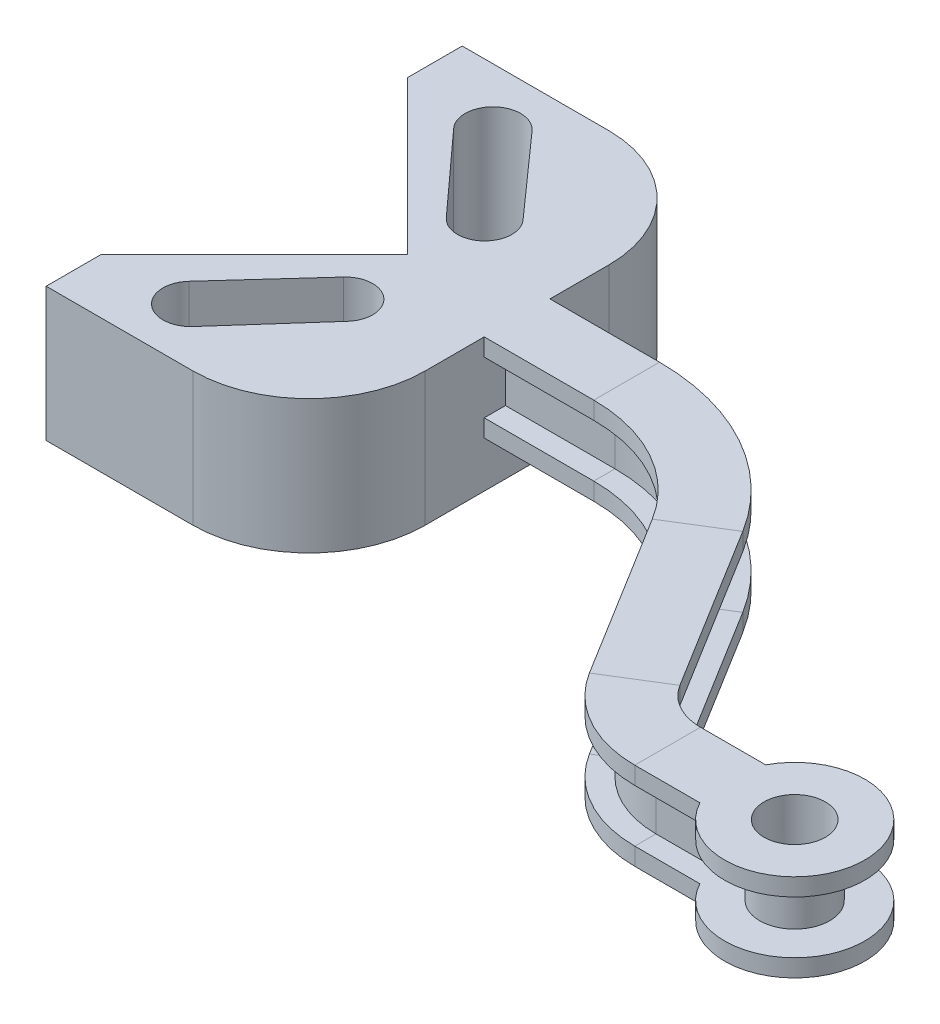
SolidWorks part; units mm, degrees
ref_plane "Front Plane" through (0, 0, 0) normal (0, 0, 1) x (1, 0, 0)
ref_plane "Top Plane" through (0, 0, 0) normal (0, 1, 0) x (1, 0, 0)
ref_plane "Right Plane" through (0, 0, 0) normal (1, 0, 0) x (0, 0, -1)
sketch "Sketch1" plane through (0, 0, 0) normal (0, 1, 0) x (1, 0, 0)
  line L0 (484.4371, 0) -> (-616.5563, 0) construction
  line L1 (-300, -132.5) -> (-132.5, -132.5)
  line L2 (-300, -132.5) -> (-300, -70.1185)
  line L3 (-300, -70.1185) -> (-125, 104.8815)
  line L4 (-125, 104.8815) -> (-610.7916, 104.8815) construction
  line L5 (-300, 342.2631) -> (-132.5, 342.2631)
  line L6 (-300, 342.2631) -> (-300, 279.8815)
  line L7 (-300, 279.8815) -> (-125, 104.8815)
  line L8 (0, 209.7631) -> (0, 0)
  arc A0 (-132.5, -132.5) -> (0, 0) centre (-132.5, 0) ccw
  arc A1 (-132.5, 342.2631) -> (0, 209.7631) centre (-132.5, 209.7631) cw
  dimension "D2" = 132.5
  dimension "D1" = 237.5
  dimension "D3" = 300
  dimension "D4" = 90
  dimension "D5" = 175
extrude "Boss-Extrude1" add sketch "Sketch1" along normal blind 152.5
sketch "Sketch2" plane through (0, 152.5, 0) normal (0, 1, 0) x (1, 0, 0)
  line L0 (-300, -70.1185) -> (-300, -132.5) construction
  line L2 (-300, -132.5) -> (-132.5, -132.5) construction
  line L3 (-223.4478, -46.1823) -> (-139.3618, 46.3059)
  line L4 (-93.2582, 4.853) -> (-176.3183, -88.5576)
  line L5 (-125, 104.8815) -> (188.3086, 104.8815) construction
  line L6 (-93.2582, 204.9101) -> (-176.3183, 298.3207)
  line L7 (-223.4478, 255.9454) -> (-139.3618, 163.4572)
  arc A0 (-223.4478, -46.1823) -> (-176.3183, -88.5576) centre (-200, -67.5) ccw
  arc A1 (-93.2582, 4.853) -> (-139.3618, 46.3059) centre (-116.4244, 25.4522) ccw
  arc A2 (-93.2582, 204.9101) -> (-139.3618, 163.4572) centre (-116.4244, 184.3109) cw
  arc A3 (-223.4478, 255.9454) -> (-176.3183, 298.3207) centre (-200, 277.2631) cw
  point P0 (-200, -67.5)
  point P1 (-116.4244, 25.4522)
  dimension "D4" = 62
  dimension "D1" = 100
  dimension "D2" = 65
  dimension "D3" = 125
extrude "Cut-Extrude1" cut sketch "Sketch2" against normal through all
sketch "Sketch3" plane through (0, 0, 0) normal (1, 0, 0) x (0, 0, -1)
  line L0 (104.8815, 152.5) -> (104.8815, -55.0634) construction
  line L2 (67.3815, 152.5) -> (142.3815, 152.5)
  line L3 (142.3815, 152.5) -> (142.3815, 132.5)
  line L4 (142.3815, 132.5) -> (118.1669, 132.5)
  line L5 (118.1669, 132.5) -> (118.1669, 72.5)
  line L6 (118.1669, 72.5) -> (142.3815, 72.5)
  line L7 (142.3815, 72.5) -> (142.3815, 52.5)
  line L8 (142.3815, 52.5) -> (67.3815, 52.5)
  line L9 (67.3815, 72.5) -> (67.3815, 52.5)
  line L10 (91.5962, 72.5) -> (67.3815, 72.5)
  line L11 (91.5962, 132.5) -> (91.5962, 72.5)
  line L12 (67.3815, 132.5) -> (91.5962, 132.5)
  line L13 (67.3815, 152.5) -> (67.3815, 132.5)
  point P11 (104.8815, 52.5)
  point P16 (0, 0)
  point P17 (0, 0)
  dimension "D1" = 37.5
  dimension "D2" = 20
  dimension "D3" = 100
sketch "Sketch4" plane through (0, 0, 0) normal (0, 1, 0) x (1, 0, 0)
  line L0 (0, 104.8815) -> (125, 104.8815)
  line L1 (307.8767, 2.9351) -> (424.1086, -185.083)
  line L2 (509.1676, -232.5) -> (654.1676, -232.5)
  line L3 (-300, -132.5) -> (-132.5, -132.5) construction
  arc A0 (125, 104.8815) -> (307.8767, 2.9351) centre (125, -110.1185) cw
  arc A1 (424.1086, -185.083) -> (509.1676, -232.5) centre (509.1676, -132.5) ccw
  dimension "D2" = 215
  dimension "D3" = 100
  dimension "D4" = 100
  dimension "D1" = 125
  dimension "D5" = 145
sweep "Sweep2" add profiles "Sketch3" path "Sketch4"
ref_plane "Plane1" through (0, 0, 232.5) normal (0, 0, 1) x (1, 0, 0)
sketch "Sketch6" plane through (0, 0, 232.5) normal (0, 0, 1) x (1, 0, 0)
  line L0 (654.1676, 152.5) -> (574.1676, 152.5)
  line L1 (509.1676, 152.5) -> (654.1676, 152.5) construction
  line L2 (574.1676, 152.5) -> (574.1676, 132.5)
  line L3 (509.1676, 132.5) -> (654.1676, 132.5) construction
  line L4 (574.1676, 132.5) -> (614.1676, 132.5)
  line L5 (614.1676, 132.5) -> (614.1676, 72.5)
  line L6 (509.1676, 72.5) -> (654.1676, 72.5) construction
  line L7 (614.1676, 72.5) -> (574.1676, 72.5)
  line L8 (574.1676, 72.5) -> (574.1676, 52.5)
  line L9 (509.1676, 52.5) -> (654.1676, 52.5) construction
  line L10 (574.1676, 52.5) -> (654.1676, 52.5)
  line L11 (654.1676, 52.5) -> (654.1676, 152.5)
  line L12 (654.1676, 152.5) -> (654.1676, 182.8913) construction
  dimension "D1" = 80
  dimension "D2" = 40
revolve "Revolve2" add sketch "Sketch6" angle 360 about L12
sketch "Sketch7" plane through (0, 152.5, 0) normal (0, 1, 0) x (1, 0, 0)
  circle A0 centre (654.1676, -232.5) radius 35
extrude "Cut-Extrude2" cut sketch "Sketch7" against normal up to surface (100 mm away)
